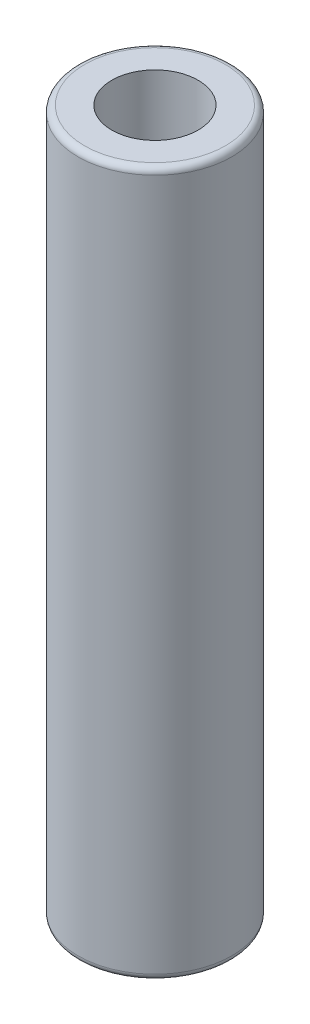
SolidWorks part; units mm, degrees
material "Chrome Stainless Steel"
ref_plane "Front" through (0, 0, 0) normal (0, 0, 1) x (1, 0, 0)
ref_plane "Top" through (0, 0, 0) normal (0, 1, 0) x (1, 0, 0)
ref_plane "Right" through (0, 0, 0) normal (1, 0, 0) x (0, 0, -1)
sketch "Sketch1" plane through (0, 0, 0) normal (0, 0, 1) x (1, 0, 0)
  line L0 (0, 543.0052) -> (0, -474.9595) construction
  line L1 (-158.2028, 0) -> (222.6643, 0) construction
  line L2 (0, 0) -> (0, 43.6753)
  line L3 (0, 43.6753) -> (8.7313, 43.6753)
  line L4 (9.525, 42.8815) -> (9.525, 0)
  line L5 (9.525, 0) -> (0, 0)
  arc A0 (9.525, 42.8815) -> (8.7313, 43.6753) centre (8.7313, 42.8815) ccw
  dimension "D3" = 0.7937
  dimension "D1" = 87.3506
  dimension "D2" = 19.05
revolve "Revolve1" add sketch "Sketch1" angle 360 about L0
hole_wizard "1/2-13 Tapped Hole1" positions "Sketch3" profile "Sketch4" tap size "1/2-13" standard "ANSI Inch"
sketch "Sketch3" plane through (0, 43.6753, 0) normal (0, 1, 0) x (1, 0, 0)
  point P0 (0, 0)
sketch "Sketch4" plane through (0, 43.6753, 0) normal (1, 0, 0) x (0, 0, 1)
  line L0 (0, 0) -> (0, 22.2695)
  line L1 (0, 22.2695) -> (5.3581, 19.05)
  line L2 (5.3581, 19.05) -> (5.3581, 0)
  line L5 (5.3581, 0) -> (0, 0)
  line L10 (0, 22.2695) -> (-5.3581, 19.05) construction
  line L11 (0, -6.35) -> (0, 107.95) construction
  dimension "Tap Drill Dia." = 10.7163
  dimension "Tap Drill Depth" = 19.05
  dimension "Drill Angle" = 118
cosmetic thread "Hole Thread1" parameters "D1"=19.05, "D2"=12.7
mirror "Mirror1" about plane through (0, 0, 0) normal (0, 1, 0) of bodies 102
